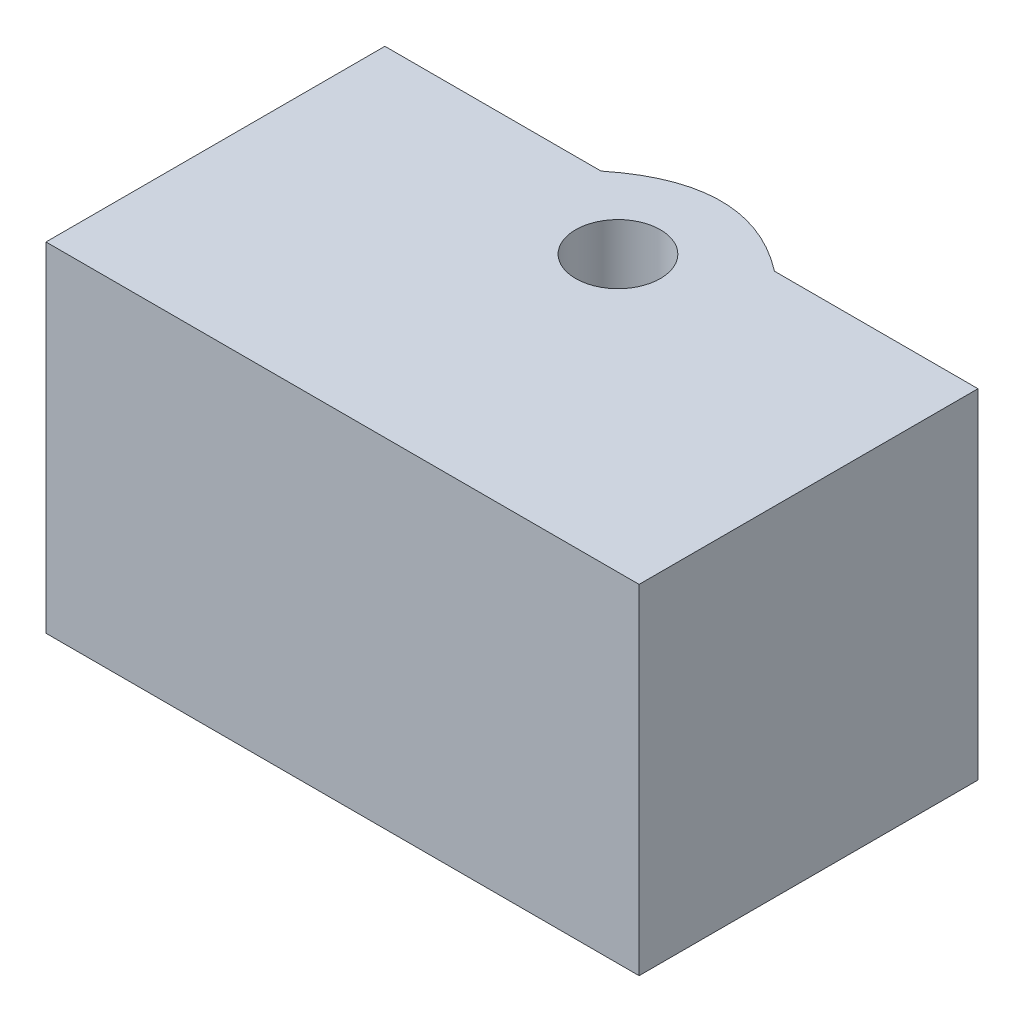
SolidWorks part; units mm, degrees
ref_plane "Front Plane" through (0, 0, 0) normal (0, 0, 1) x (1, 0, 0)
ref_plane "Top Plane" through (0, 0, 0) normal (0, 1, 0) x (1, 0, 0)
ref_plane "Right Plane" through (0, 0, 0) normal (1, 0, 0) x (0, 0, -1)
sketch "Sketch1" plane through (0, 0, 0) normal (0, 1, 0) x (1, 0, 0)
  line L0 (-16.5729, 3.7454) -> (-16.5729, -16.2546)
  line L1 (-16.5729, -16.2546) -> (18.4271, -16.2546)
  line L2 (18.4271, -16.2546) -> (18.4271, 3.7454)
  line L3 (18.4271, 3.7454) -> (6.4153, 3.7454)
  line L4 (-16.5729, 3.7454) -> (-3.8195, 3.7454)
  circle A0 centre (0.9271, 0) radius 2.5
  spline S0 degree 2 poles (-3.8195, 3.7454) (1.1986, 7.7662) (6.4153, 3.7454) knots 0 0 0 1 1 1
  dimension "D1" = 5
  dimension "D2" = 35
  dimension "D3" = 17.5
  dimension "D4" = 20
extrude "Boss-Extrude1" add sketch "Sketch1" along normal blind 20
